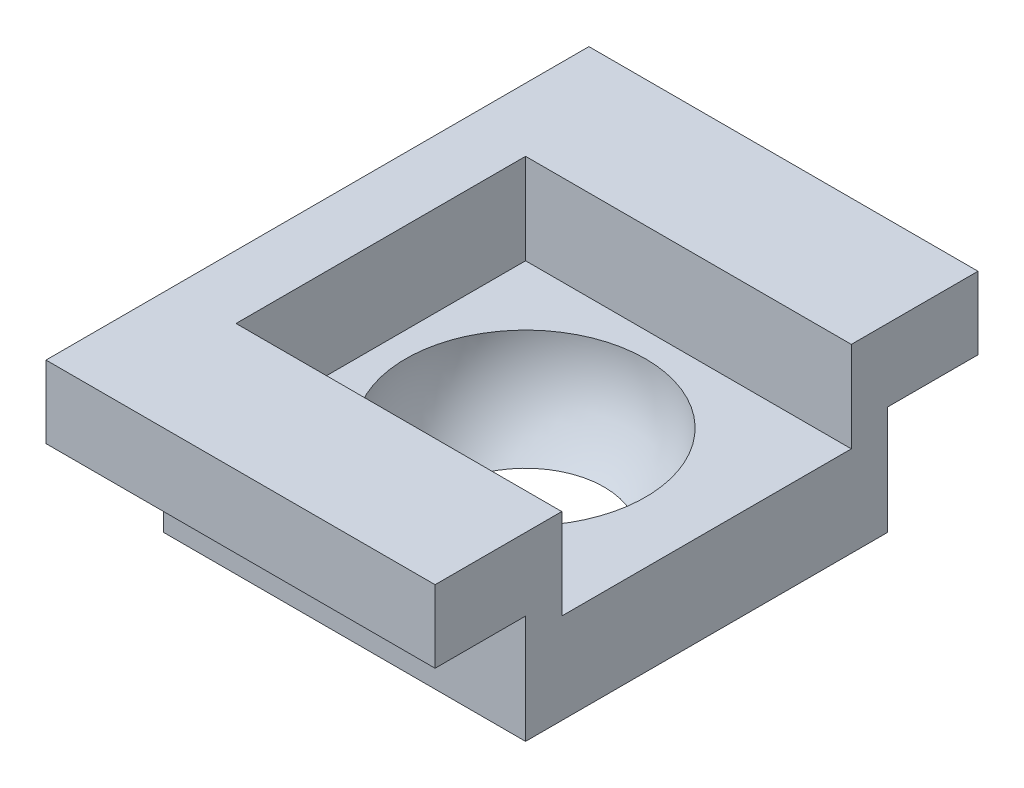
SolidWorks part; units mm, degrees
ref_plane "Front Plane" through (0, 0, 0) normal (0, 0, 1) x (1, 0, 0)
ref_plane "Top Plane" through (0, 0, 0) normal (0, 1, 0) x (1, 0, 0)
ref_plane "Right Plane" through (0, 0, 0) normal (1, 0, 0) x (0, 0, -1)
sketch "Sketch1" plane through (0, 0, 0) normal (0, 1, 0) x (1, 0, 0)
  line L1 (-2.306, 2.016) -> (1.694, 2.016)
  line L2 (-2.306, 2.016) -> (-2.306, -1.984)
  line L3 (-2.306, -1.984) -> (1.694, -1.984)
  line L4 (1.694, 2.016) -> (1.694, -1.984)
  dimension "D1" = 4
  dimension "D2" = 4
extrude "Boss-Extrude1" add sketch "Sketch1" along normal blind 2
sketch "Sketch2" plane through (0, 2, 0) normal (0, 1, 0) x (1, 0, 0)
  line L0 (1.694, 2.016) -> (-2.306, 2.016) construction
  line L1 (-2.306, 2.016) -> (-2.306, -1.984) construction
  line L2 (-0.306, -1.309) -> (-0.306, 1.341)
  arc A0 (-0.306, 1.341) -> (-0.306, -1.309) centre (-0.306, 0.016) ccw
  dimension "D3" = 2.65
  dimension "D1" = 2
  dimension "D2" = 2
revolve "Cut-Revolve1" cut sketch "Sketch2" angle 360 about L2
sketch "Sketch3" plane through (0, 0, 0) normal (0, -1, 0) x (1, 0, 0)
  line L1 (-4.7173, 2.6241) -> (2.2784, 2.6241)
  line L2 (-4.7173, 2.6241) -> (-4.7173, -2.1717)
  line L3 (-4.7173, -2.1717) -> (2.2784, -2.1717)
  line L4 (2.2784, 2.6241) -> (2.2784, -2.1717)
extrude "Cut-Extrude1" cut sketch "Sketch3" against normal blind 1
sketch "Sketch4" plane through (0, 2, 0) normal (0, 1, 0) x (1, 0, 0)
  line L0 (-2.306, -1.984) -> (1.694, -1.984) construction
  line L1 (-1.906, -1.584) -> (1.515, -1.584)
  line L2 (-1.906, -1.584) -> (-1.906, 1.616)
  line L3 (-1.906, 1.616) -> (1.515, 1.616)
  line L5 (1.694, 2.016) -> (-2.306, 2.016) construction
  line L6 (-2.306, 2.016) -> (-2.306, -1.984) construction
  line L7 (1.515, -1.584) -> (1.694, -1.584)
  line L8 (-2.306, -1.984) -> (1.694, -1.984)
  line L9 (-2.306, -1.984) -> (-2.306, 2.016)
  line L10 (-2.306, 2.016) -> (1.694, 2.016)
  line L11 (1.694, -1.984) -> (1.694, -1.584)
  line L12 (1.515, 1.616) -> (1.694, 1.616)
  line L13 (1.694, 1.616) -> (1.694, 2.016)
  dimension "D1" = 0.4
  dimension "D2" = 0.4
  dimension "D3" = 0.4
  dimension "D4" = 0.4
extrude "Boss-Extrude2" add sketch "Sketch4" along normal blind 1
sketch "Sketch5" plane through (0, 0, 1.984) normal (0, 0, 1) x (1, 0, 0)
  line L5 (1.694, 3) -> (1.694, 1) construction
  line L6 (-2.306, 3) -> (1.694, 3)
  line L7 (-2.306, 3) -> (-2.306, 2.2)
  line L8 (-2.306, 2.2) -> (1.694, 2.2)
  line L9 (1.694, 3) -> (1.694, 2.2)
  dimension "D1" = 0.8
extrude "Boss-Extrude3" add sketch "Sketch5" along normal blind 1
sketch "Sketch6" plane through (0, 0, -2.016) normal (0, 0, -1) x (-1, 0, 0)
  line L0 (2.306, 3) -> (2.306, 1) construction
  line L1 (-1.694, 3) -> (2.306, 3)
  line L2 (-1.694, 3) -> (-1.694, 2.2)
  line L3 (-1.694, 2.2) -> (2.306, 2.2)
  line L4 (2.306, 3) -> (2.306, 2.2)
  dimension "D1" = 0.8
extrude "Boss-Extrude4" add sketch "Sketch6" along normal blind 1
sketch "Sketch9" plane through (-2.306, 0, 0) normal (-1, 0, 0) x (0, 0, 1)
  line L1 (-3.016, 3) -> (2.984, 3)
  line L2 (-3.016, 3) -> (-3.016, 2.2)
  line L3 (-3.016, 2.2) -> (2.984, 2.2)
  line L4 (2.984, 3) -> (2.984, 2.2)
extrude "Boss-Extrude6" add sketch "Sketch9" along normal blind 0.3
